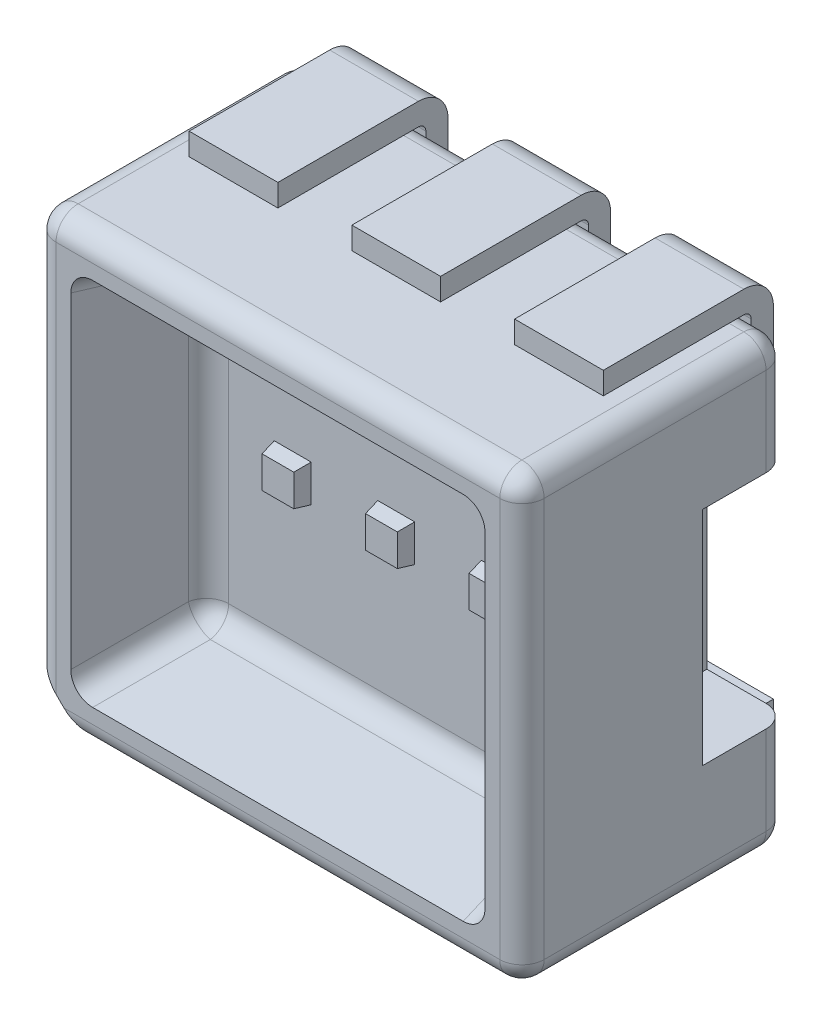
SolidWorks part; units mm, degrees
ref_plane "Front Plane" through (0, 0, 0) normal (0, 0, 1) x (1, 0, 0)
ref_plane "Top Plane" through (0, 0, 0) normal (0, 1, 0) x (1, 0, 0)
ref_plane "Right Plane" through (0, 0, 0) normal (1, 0, 0) x (0, 0, -1)
sketch "Sketch1" plane through (0, 0, 0) normal (0, 0, 1) x (1, 0, 0)
  line L1 (0, 0) -> (3.3, 0)
  line L2 (0, 0) -> (0, 3)
  line L3 (0, 3) -> (3.3, 3)
  line L4 (3.3, 0) -> (3.3, 3)
  dimension "D1" = 3
  dimension "D2" = 3.3
extrude "Boss-Extrude1" add sketch "Sketch1" along normal blind 1.8
sketch "Sketch4" plane through (0, 0, 1.8) normal (0, 0, 1) x (1, 0, 0)
  line L0 (0, 0.3536) -> (0.3536, 0)
  line L1 (0, 3) -> (0, 0) construction
  line L2 (0, 0) -> (3.3, 0) construction
  line L3 (0.3536, 0) -> (0, 0)
  line L4 (0, 0) -> (0, 0.3536)
  dimension "D1" = 45
  dimension "D2" = 0.5
extrude "Cut-Extrude2" cut sketch "Sketch4" against normal blind 0.4
sketch "Sketch2" plane through (0, 0, 1.8) normal (0, 0, 1) x (1, 0, 0)
  line L0 (1.65, 3) -> (1.65, 0) construction
  line L3 (3.3, 3) -> (0, 3) construction
  line L5 (0.3536, 0) -> (3.3, 0) construction
  line L7 (0.25, 2.75) -> (3.05, 2.75)
  line L8 (0.25, 2.75) -> (0.25, 0.25)
  line L9 (0.25, 0.25) -> (3.05, 0.25)
  line L10 (3.05, 2.75) -> (3.05, 0.25)
  line L12 (3.3, 0) -> (3.3, 3) construction
  line L13 (3.3, 1.5) -> (0, 1.5) construction
  line L14 (0, 3) -> (0, 0.3536) construction
  point P7 (3.05, 1.5)
  point P16 (1.65, 2.75)
  dimension "D1" = 2.8
  dimension "D2" = 2.5
extrude "Cut-Extrude1" cut sketch "Sketch2" against normal blind 0.8 draft 10
fillet "Fillet1" radius 0.15 20 edges at (1.65, 2.6089, 1) (0.3911, 1.5, 1) (1.65, 0.3911, 1) (2.9089, 1.5, 1) (2.9795, 0.3205, 1.4) (0.3205, 0.3205, 1.4) (2.9795, 2.6795, 1.4) (0.3205, 2.6795, 1.4) (1.8268, 0, 1.8) (3.3, 1.5, 1.8) (1.65, 3, 1.8) (0, 1.6768, 1.8) (1.65, 3, 0) (1.65, 0, 0) (3.3, 1.5, 0) (0, 1.5, 0) (0, 0, 0.7) (3.3, 0, 0.9) (3.3, 3, 0.9) (0, 3, 0.9)
ref_plane "Plane1" through (0.55, 0, 0) normal (1, 0, 0) x (0, 0, -1)
sketch "Sketch3" plane through (0.55, 0, 0) normal (1, 0, 0) x (0, 0, -1)
  line L0 (-1, 3) -> (0, 3)
  line L1 (-1.65, 3) -> (-0.15, 3) construction
  line L2 (0, 3) -> (0, 2.35)
  line L3 (0, 2.85) -> (0, 0.15) construction
  line L4 (-1.8, 0.15) -> (-1.8, 2.85) construction
  dimension "D1" = 1
  dimension "D2" = 0.65
  dimension "D3" = 0.8
extrude "Extrude-Thin1" add sketch "Sketch3" along normal mid plane 0.6 thin thin type one direction reverse wall 0.15
pattern_linear "LPattern1" count 3 spacing 1.1 along (1, 0, 0) of "Extrude-Thin1"
ref_plane "Plane2" through (0, 1.5, 0) normal (0, 1, 0) x (1, 0, 0)
mirror "Mirror1" about plane through (0, 1.5, 0) normal (0, 1, 0) of "LPattern1", "Extrude-Thin1"
sketch "Sketch5" plane through (0, 0, 1.4) normal (0, 0, 1) x (1, 0, 0)
  line L0 (0.15, 0) -> (0.3536, 0) construction
  line L1 (0, 0.3536) -> (0, 0.15) construction
  circle A0 centre (0.11, 0.11) radius 0.04
  dimension "D3" = 0.08
  dimension "D1" = 0.11
  dimension "D2" = 0.11
extrude "Cut-Extrude3" cut sketch "Sketch5" against normal blind 0.1
sketch "Sketch6" plane through (0, 0, 1) normal (0, 0, 1) x (1, 0, 0)
  line L0 (0.5169, 1.5) -> (2.7831, 1.5) construction
  line L1 (0.5169, 2.4831) -> (0.5169, 0.5169) construction
  line L2 (2.7831, 0.5169) -> (2.7831, 2.4831) construction
  line L3 (0.95, 1.625) -> (0.95, 1.375) construction
  line L4 (2.7831, 2.4831) -> (0.5169, 2.4831) construction
  line L5 (1.65, 2.4831) -> (1.65, 0.5169) construction
  line L6 (0.5169, 0.5169) -> (2.7831, 0.5169) construction
  line L7 (0.825, 1.625) -> (1.075, 1.625)
  line L8 (0.825, 1.625) -> (0.825, 1.375)
  line L9 (0.825, 1.375) -> (1.075, 1.375)
  line L10 (1.075, 1.625) -> (1.075, 1.375)
  point P16 (1.075, 1.5)
  dimension "D1" = 0.25
  dimension "D2" = 0.25
  dimension "D3" = 0.7
extrude "Boss-Extrude2" add sketch "Sketch6" along normal blind 0.1 draft 10
pattern_linear "LPattern2" count 3 spacing 0.7 along (1, 0, 0) of "Boss-Extrude2"
sketch "Sketch7" plane through (0, 1.5, 0) normal (0, 1, 0) x (1, 0, 0)
  line L0 (0, -0.58) -> (0, 0)
  line L1 (0, -1.65) -> (0, -0.15) construction
  line L2 (0, 0) -> (0.55, 0)
  line L3 (3.15, -1.8) -> (0.15, -1.8) construction
  line L4 (0.55, -0.58) -> (0, -0.58)
  line L5 (0.55, 0) -> (0.55, -0.58)
  dimension "D1" = 1.22
  dimension "D2" = 0.55
ref_plane "Plane3" through (1.65, 0, 0) normal (1, 0, 0) x (0, 0, -1)
extrude "Cut-Extrude4" cut sketch "Sketch7" against normal mid plane 1.5
mirror "Mirror2" about plane through (1.65, 0, 0) normal (1, 0, 0) of "Cut-Extrude4"
